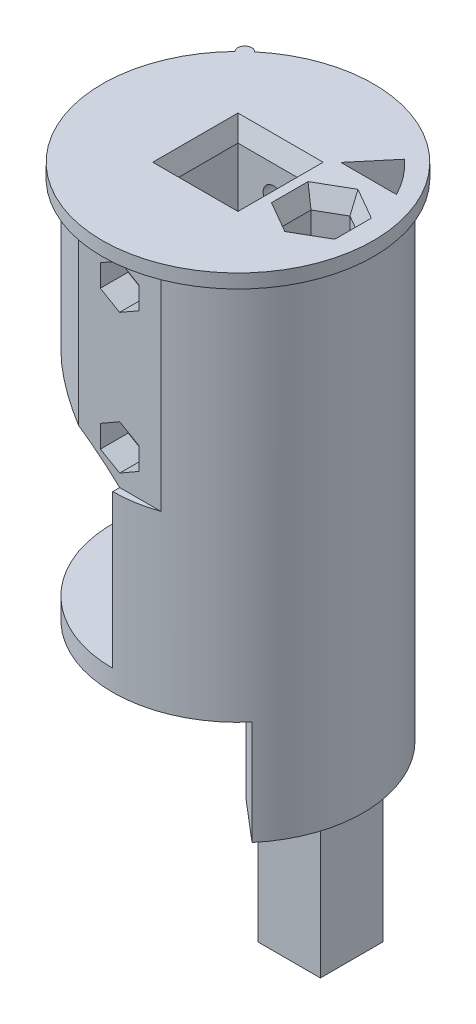
SolidWorks part; units mm, degrees
ref_plane "Спереди" through (0, 0, 0) normal (0, 0, 1) x (1, 0, 0)
ref_plane "Сверху" through (0, 0, 0) normal (0, 1, 0) x (1, 0, 0)
ref_plane "Справа" through (0, 0, 0) normal (1, 0, 0) x (0, 0, -1)
sketch "Эскиз1" plane through (0, 0, 0) normal (0, 1, 0) x (1, 0, 0)
  circle A0 centre (0, 0) radius 18
  dimension "D1" = 36
extrude "Бобышка-Вытянуть1" add sketch "Эскиз1" along normal blind 55
sketch "Эскиз2" plane through (0, 55, 0) normal (0, 1, 0) x (1, 0, 0)
  circle A0 centre (0, 0) radius 19.5
  dimension "D1" = 39
extrude "Бобышка-Вытянуть2" add sketch "Эскиз2" along normal blind 2
sketch "Эскиз3" plane through (0, 57, 0) normal (0, 1, 0) x (1, 0, 0)
  line L1 (-5.125, -5.125) -> (5.125, -5.125)
  line L2 (-5.125, -5.125) -> (-5.125, 5.125)
  line L3 (-5.125, 5.125) -> (5.125, 5.125)
  line L4 (5.125, -5.125) -> (5.125, 5.125)
  line L5 (-5.125, -5.125) -> (5.125, 5.125) construction
  line L6 (-5.125, 5.125) -> (5.125, -5.125) construction
  point P0 (0, 0)
  dimension "D1" = 10.25
extrude "Вырез-Вытянуть1" cut sketch "Эскиз3" against normal blind 40
sketch "Эскиз4" plane through (0, 0, 0) normal (0, -1, 0) x (1, 0, 0)
  line L0 (0, 0) -> (11.5702, 13.7888) construction
  line L1 (0, 0) -> (11.5702, -13.7888) construction
  line L2 (11.5702, 13.7888) -> (11.5702, -13.7888) construction
  line L3 (0, 0) -> (13.6996, 11.6756) construction
  line L5 (5.1423, -6.1284) -> (11.5702, -13.7888)
  line L6 (5.1423, -6.1284) -> (5.1423, 4.3826)
  line L7 (5.1423, 4.3826) -> (13.6996, 11.6756)
  circle A3 centre (0, 0) radius 18 construction
  arc A4 (13.6996, 11.6756) -> (11.5702, -13.7888) centre (0, 0) cw
  point P5 (11.5702, 13.7888)
  point P8 (11.5702, -13.7888)
  dimension "D1" = 100
  dimension "D2" = 3
  dimension "D3" = 10
extrude "Бобышка-Вытянуть3" add sketch "Эскиз4" along normal blind 15
sketch "Sketch1" plane through (0, -15, 0) normal (0, -1, 0) x (1, 0, 0)
  circle A0 centre (0, 0) radius 18
  arc A3 (13.6996, 11.6756) -> (11.5702, -13.7888) centre (0, 0) ccw construction
extrude "Boss-Extrude1" add sketch "Sketch1" along normal blind 20
sketch "Sketch3" plane through (0, -35, 0) normal (0, -1, 0) x (1, 0, 0)
  circle A0 centre (0, 0) radius 18
  circle A3 centre (0, 0) radius 18 construction
extrude "Boss-Extrude2" add sketch "Sketch3" along normal blind 7
sketch "Sketch4" plane through (0, -42, 0) normal (0, -1, 0) x (1, 0, 0)
  line L1 (5.1, 5.1) -> (-5.1, 5.1)
  line L2 (5.1, 5.1) -> (5.1, -5.1)
  line L3 (5.1, -5.1) -> (-5.1, -5.1)
  line L4 (-5.1, 5.1) -> (-5.1, -5.1)
  line L5 (5.1, 5.1) -> (-5.1, -5.1) construction
  line L6 (5.1, -5.1) -> (-5.1, 5.1) construction
  point P0 (0, 0)
  dimension "D1" = 10.2
  dimension "D2" = 10.2
extrude "Cut-Extrude2" cut sketch "Sketch4" against normal blind 27
sketch "Sketch6" plane through (0, 0, 0) normal (0, -1, 0) x (1, 0, 0)
  line L0 (0, 18) -> (0, -18) construction
  line L1 (0, 18) -> (0, -18)
  arc A0 (13.6996, 11.6756) -> (11.5702, -13.7888) centre (0, 0) ccw construction
  arc A1 (0, -18) -> (0, 18) centre (0, 0) cw
extrude "Cut-Extrude4" cut sketch "Sketch6" against normal blind 25
sketch "Sketch8" plane through (0, 0, 0) normal (0, -1, 0) x (1, 0, 0)
  line L0 (0, -18) -> (0, 18)
  arc A0 (0, -18) -> (0, 18) centre (0, 0) cw
  arc A1 (13.6996, 11.6756) -> (0, 18) centre (0, 0) ccw construction
extrude "Boss-Extrude3" add sketch "Sketch8" against normal blind 3
sketch "Sketch9" plane through (0, 0, 0) normal (-1, 0, 0) x (0, 0, 1)
  line L0 (-18, 3) -> (18, 25) construction
  line L2 (18, 25) -> (-18, 25)
  line L3 (18, 25) -> (18, 3)
  line L4 (18, 3) -> (-18, 3)
  line L5 (-18, 25) -> (-18, 3)
  line L6 (18, 25) -> (-18, 3) construction
  line L7 (18, 3) -> (-18, 25) construction
  point P4 (0, 14)
extrude "Cut-Extrude5" cut sketch "Sketch9" against normal blind 8
sketch "Sketch10" plane through (0, 0, 0) normal (0, -1, 0) x (1, 0, 0)
  line L0 (0, -18) -> (0, 18) construction
  line L2 (1.5, 8.7) -> (-1.5, 8.7)
  line L3 (1.5, 8.7) -> (1.5, 6.7)
  line L4 (1.5, 6.7) -> (-1.5, 6.7)
  line L5 (-1.5, 8.7) -> (-1.5, 6.7)
  line L6 (1.5, 8.7) -> (-1.5, 6.7) construction
  line L7 (1.5, 6.7) -> (-1.5, 8.7) construction
  circle A0 centre (0, 0) radius 3.7
  arc A1 (13.6996, 11.6756) -> (11.5702, -13.7888) centre (0, 0) ccw construction
  point P9 (0, 7.7)
  point P14 (0, 3.7)
  dimension "D1" = 7.4
  dimension "D2" = 2
  dimension "D3" = 3
  dimension "D4" = 4
extrude "Cut-Extrude6" cut sketch "Sketch10" against normal blind 10
sketch "Sketch11" plane through (0, -42, 0) normal (0, -1, 0) x (1, 0, 0)
  line L0 (-18, 0) -> (18, 0) construction
  circle A0 centre (0, 0) radius 18 construction
  circle A1 centre (12, 0) radius 2
  dimension "D1" = 4
  dimension "D2" = 6
extrude "Cut-Extrude7" cut sketch "Sketch11" against normal blind 102
sketch "Sketch15" plane through (0, -42, 0) normal (0, -1, 0) x (1, 0, 0)
  circle A0 centre (0, 0) radius 18
  circle A3 centre (0, 0) radius 18 construction
extrude "Cut-Extrude9" cut sketch "Sketch15" against normal blind 27
sketch "Sketch17" plane through (0, 25, 0) normal (0, -1, 0) x (1, 0, 0)
  line L2 (-18, 0) -> (14.8, 0) construction
  line L3 (14.8, 0) -> (13.8, 0) construction
  line L4 (0, 18) -> (0, -18) construction
  line L6 (5.9161, -17) -> (-5.9161, -17)
  line L7 (5.9161, 17) -> (-5.9161, 17)
  arc A0 (8, 16.1245) -> (8, -16.1245) centre (0, 0) ccw construction
  arc A1 (-5.9161, -17) -> (5.9161, -17) centre (0, 0) ccw
  arc A2 (-5.9161, 17) -> (5.9161, 17) centre (0, 0) cw
  point P14 (13.8, 0)
  point P20 (0, -17)
  point P23 (0, 17)
  dimension "D4" = 1
extrude "Cut-Extrude11" cut sketch "Sketch17" against normal blind 30
sketch "Sketch18" plane through (0, 0, -17) normal (0, 0, 1) x (1, 0, 0)
  line L0 (0, 25) -> (0, 55) construction
  line L1 (5.9161, 25) -> (-5.9161, 25) construction
  line L2 (5.9161, 55) -> (-5.9161, 55) construction
  circle A0 centre (0, 30) radius 1.5
  circle A1 centre (0, 50) radius 1.5
  point P3 (0, 40)
  dimension "D1" = 3
  dimension "D2" = 10
  dimension "D3" = 20
extrude "Cut-Extrude12" cut sketch "Sketch18" along normal through all
sketch "Sketch19" plane through (0, 0, -17) normal (0, 0, 1) x (1, 0, 0)
  circle A0 centre (0, 30) radius 3
  circle A1 centre (0, 50) radius 3
  dimension "D1" = 6
extrude "Cut-Extrude13" cut sketch "Sketch19" along normal blind 3
sketch "Sketch23" plane through (0, 3, 0) normal (0, 1, 0) x (1, 0, 0)
  line L0 (0, 18) -> (0, -18) construction
  line L1 (0, -14.4) -> (8, -14.4)
  line L2 (8, 16.1245) -> (8, -16.1245) construction
  line L3 (0, 14.4) -> (8, 14.4)
  line L4 (0, -14.4) -> (0, -18)
  line L5 (0, 14.4) -> (0, 18)
  line L6 (8, -14.4) -> (8, -16.1245)
  line L7 (8, 16.1245) -> (8, 14.4)
  arc A0 (8, 16.1245) -> (8, -16.1245) centre (0, 0) ccw construction
  arc A1 (0, -18) -> (8, -16.1245) centre (0, 0) ccw
  arc A2 (0, 18) -> (8, 16.1245) centre (0, 0) cw
  arc A3 (-5.9161, 17) -> (-5.9161, -17) centre (0, 0) ccw construction
  arc A4 (11.5702, 13.7888) -> (13.6996, -11.6756) centre (0, 0) ccw construction
  dimension "D1" = 3.6
extrude "Boss-Extrude5" add sketch "Sketch23" along normal blind 22
sketch "Sketch25" plane through (0, 0, 17) normal (0, 0, 1) x (1, 0, 0)
  line L0 (0, 55) -> (0, 25) construction
  line L1 (2.7713, 28.4) -> (2.7713, 31.6)
  line L2 (2.7713, 31.6) -> (0, 33.2)
  line L3 (0, 33.2) -> (-2.7713, 31.6)
  line L4 (-2.7713, 31.6) -> (-2.7713, 28.4)
  line L5 (-2.7713, 28.4) -> (0, 26.8)
  line L6 (0, 26.8) -> (2.7713, 28.4)
  line L7 (-5.9161, 55) -> (5.9161, 55) construction
  line L9 (-2.7821, 48.4189) -> (-0.0218, 46.8001)
  line L10 (-0.0218, 46.8001) -> (2.7603, 48.3811)
  line L11 (2.7603, 48.3811) -> (2.7821, 51.5811)
  line L12 (2.7821, 51.5811) -> (0.0218, 53.1999)
  line L13 (0.0218, 53.1999) -> (-2.7603, 51.6189)
  line L14 (-2.7603, 51.6189) -> (-2.7821, 48.4189)
  circle A0 centre (0, 30) radius 3.2 construction
  circle A1 centre (0, 50) radius 3.2 construction
  point P24 (0, 40)
  dimension "D1" = 6.4
  dimension "D2" = 20
  dimension "D3" = 10
extrude "Cut-Extrude16" cut sketch "Sketch25" against normal blind 4
sketch "Sketch26" plane through (0, 57, 0) normal (0, 1, 0) x (1, 0, 0)
  line L0 (14.8, 0) -> (5.125, 0) construction
  line L2 (8.4493, -2.05) -> (12, -4.1)
  line L3 (12, -4.1) -> (15.5507, -2.05)
  line L4 (15.5507, -2.05) -> (15.5507, 2.05)
  line L5 (15.5507, 2.05) -> (12, 4.1)
  line L6 (12, 4.1) -> (8.4493, 2.05)
  line L7 (5.125, -5.125) -> (5.125, 5.125) construction
  line L8 (8.4493, 2.05) -> (8.4493, -2.05)
  circle A0 centre (12, 0) radius 4.1 construction
  point P2 (15.5507, 0)
  dimension "D1" = 8.2
extrude "Cut-Extrude17" cut sketch "Sketch26" against normal blind 25.4
sketch "Sketch27" plane through (0, 0, 17) normal (0, 0, 1) x (1, 0, 0)
  line L0 (0, 25) -> (-20, 36.547) construction
  line L1 (-20, 36.547) -> (-20, 25)
  line L2 (-20, 25) -> (0, 25)
  line L3 (-18, 25) -> (-5.9161, 25) construction
  line L4 (-5.9161, 25) -> (0, 25) construction
  arc A0 (0, 25) -> (-20, 36.547) centre (-34.3242, -11.3572) ccw
  dimension "D3" = 50
  dimension "D1" = 30
  dimension "D2" = 20
extrude "Cut-Extrude18" cut sketch "Sketch27" against normal through all
fillet "Fillet2" radius 5 2 edges at (8, 14, 14.4) (8, 14, -14.4)
sketch "Sketch30" plane through (8, 0, 0) normal (-1, 0, 0) x (0, 0, 1)
  line L0 (-9.4, 8) -> (9.4, 8) construction
  line L1 (-9.4, 25) -> (-9.4, 3) construction
  line L2 (9.4, 3) -> (9.4, 25) construction
  line L4 (9.4, 13) -> (-9.4, 13)
  line L5 (9.4, 13) -> (9.4, 3)
  line L6 (9.4, 3) -> (-9.4, 3)
  line L7 (-9.4, 13) -> (-9.4, 3)
  line L8 (9.4, 13) -> (-9.4, 3) construction
  line L9 (9.4, 3) -> (-9.4, 13) construction
  point P6 (0, 8)
  dimension "D1" = 10
extrude "Cut-Extrude20" cut sketch "Sketch30" against normal blind 3
chamfer "Chamfer1" distance 1 angle 70 4 edges at (5.125, 57, 0) (0, 57, 5.125) (-5.125, 57, 0) (0, 57, -5.125)
chamfer "Chamfer2" distance 1 angle 70 6 edges at (15.5507, 57, 0) (13.7754, 57, 3.075) (13.7754, 57, -3.075) (10.2246, 57, -3.075) (8.4493, 57, 0) (10.2246, 57, 3.075)
sketch "Sketch37" plane through (0, -15, 0) normal (0, -1, 0) x (1, 0, 0)
  line L0 (5.1423, -0.8729) -> (17.9788, -0.8729) construction
  line L1 (5.1423, 4.3826) -> (5.1423, -6.1284) construction
  line L3 (15.4788, 3.6271) -> (6.4788, 3.6271)
  line L4 (15.4788, 3.6271) -> (15.4788, -5.3729)
  line L5 (15.4788, -5.3729) -> (6.4788, -5.3729)
  line L6 (6.4788, 3.6271) -> (6.4788, -5.3729)
  line L7 (15.4788, 3.6271) -> (6.4788, -5.3729) construction
  line L8 (15.4788, -5.3729) -> (6.4788, 3.6271) construction
  arc A0 (11.5702, -13.7888) -> (13.6996, 11.6756) centre (0, 0) ccw construction
  circle A1 centre (12, 0) radius 2
  point P8 (10.9788, -0.8729)
  dimension "D1" = 9
  dimension "D2" = 7
extrude "Boss-Extrude7" add sketch "Sketch37" along normal blind 20
sketch "Sketch38" plane through (0, -15, 0) normal (0, -1, 0) x (1, 0, 0)
  line L0 (5.1423, -6.1284) -> (5.1423, 4.3826)
  arc A0 (5.1423, -6.1284) -> (5.1423, 4.3826) centre (-10.9482, -0.8729) ccw
extrude "Cut-Extrude22" cut sketch "Sketch38" against normal up to surface (15 mm away) up to face at (0, 0, 7.7)
sketch "Sketch39" plane through (0, -15, 0) normal (0, -1, 0) x (1, 0, 0)
  line L0 (7.4207, -7.3729) -> (15.4207, -7.3729)
  line L1 (7.4207, -7.3729) -> (11.5989, -12.3522)
  line L2 (5.1423, -6.1284) -> (11.5702, -13.7888) construction
  line L3 (6.4788, -5.3729) -> (15.4788, -5.3729) construction
  line L4 (6.1866, -7.3729) -> (16.4207, -7.3729) construction
  arc A0 (11.5989, -12.3522) -> (15.4207, -7.3729) centre (-0.5503, 0.9293) ccw
  arc A1 (11.5702, -13.7888) -> (13.6996, 11.6756) centre (0, 0) ccw construction
  point P11 (11.4207, -7.3729)
  dimension "D1" = 8
  dimension "D2" = 2
  dimension "D3" = 6.5
  dimension "D4" = 5
  dimension "D6" = 50
extrude "Cut-Extrude23" cut sketch "Sketch39" against normal through all
sketch "Sketch40" plane through (0, 3, 0) normal (0, 1, 0) x (1, 0, 0)
  line L0 (7.4207, 7.3729) -> (7.4207, 11.736)
  line L1 (7.4207, 11.736) -> (11.7839, 11.736)
  line L2 (11.7839, 11.736) -> (11.7839, 7.3729)
  line L3 (11.7839, 7.3729) -> (7.4207, 7.3729)
  line L4 (7.4207, 7.3729) -> (11, 7.3729) construction
  arc A1 (8, 9.4) -> (3, 14.4) centre (3, 9.4) ccw construction
extrude "Cut-Extrude24" cut sketch "Sketch40" along normal up to surface (10 mm away) up to face at (9.8333, 13, 0.6757)
fillet "Fillet7" radius 6 2 edges at (5.1423, -7.5, 4.3826) (5.1423, -7.5, -6.1284)
sketch "Sketch41" plane through (0, 57, 0) normal (0, 1, 0) x (1, 0, 0)
  line L0 (0, 0) -> (0, 19.5) construction
  line L1 (0, 0) -> (-12.5344, 14.9379) construction
  line L2 (-12.5344, 14.9379) -> (0, 19.5) construction
  line L3 (-13.9985, 13.5754) -> (-12.5344, 14.9379)
  circle A0 centre (0, 0) radius 19.5 construction
  arc A1 (-12.5344, 14.9379) -> (-13.9985, 13.5754) centre (-13.2664, 14.2566) ccw
  dimension "D2" = 1
  dimension "D3" = 2
  dimension "D1" = 40
extrude "Boss-Extrude8" add sketch "Sketch41" against normal up to surface (2 mm away) up to face at (0, 55, 0)
sketch "Sketch42" plane through (0, 13, 0) normal (0, -1, 0) x (1, 0, 0)
  line L0 (8, -8.0632) -> (7.4207, -11.736)
  line L1 (7.4207, -11.736) -> (11.0819, -11.736)
  line L2 (11.0819, -11.736) -> (8, -8.0632)
extrude "Cut-Extrude25" cut sketch "Sketch42" against normal up to surface (12 mm away) up to face at (4.4417, 25, -1.7545)
